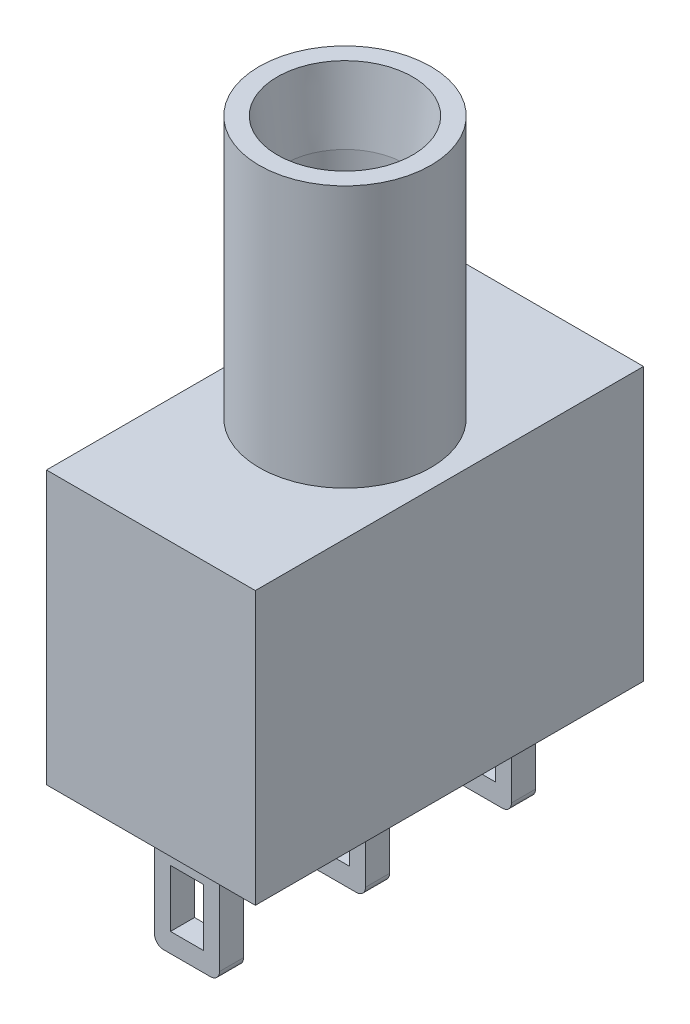
SolidWorks part; units mm, degrees
ref_plane "Plan de face" through (0, 0, 0) normal (0, 0, 1) x (1, 0, 0)
ref_plane "Plan de dessus" through (0, 0, 0) normal (0, 1, 0) x (1, 0, 0)
ref_plane "Plan de droite" through (0, 0, 0) normal (1, 0, 0) x (0, 0, -1)
sketch "Esquisse1" plane through (0, 0, 0) normal (0, 1, 0) x (1, 0, 0)
  line L1 (0, 0) -> (6.94, 0)
  line L2 (0, 0) -> (0, 12.9)
  line L3 (0, 12.9) -> (6.94, 12.9)
  line L4 (6.94, 0) -> (6.94, 12.9)
  dimension "D1" = 12.9
  dimension "D2" = 6.94
extrude "Boss.-Extru.1" add sketch "Esquisse1" along normal blind 9.06
sketch "Esquisse2" plane through (0, 9.06, 0) normal (0, 1, 0) x (1, 0, 0)
  line L0 (3.47, 12.9) -> (3.47, 0) construction
  line L1 (6.94, 12.9) -> (0, 12.9) construction
  line L2 (0, 0) -> (6.94, 0) construction
  circle A0 centre (3.47, 6.45) radius 2.85
  dimension "D1" = 5.7
extrude "Boss.-Extru.2" add sketch "Esquisse2" along normal blind 8.7
sketch "Esquisse3" plane through (0, 17.76, 0) normal (0, 1, 0) x (1, 0, 0)
  circle A0 centre (3.47, 6.45) radius 2
  dimension "D1" = 4
extrude "Enlèv. mat.-Extru.1" cut sketch "Esquisse3" against normal blind 8.7
sketch "Esquisse4" plane through (0, 0, 0) normal (-1, 0, 0) x (0, 0, 1)
  line L0 (-6.45, 0) -> (-6.45, 19.6396) construction
  line L1 (-12.9, 0) -> (0, 0) construction
  line L2 (-3.6, 17.76) -> (-9.3, 17.76) construction
  circle A0 centre (-6.4533, 14.76) radius 0.5
  dimension "D2" = 1
  dimension "D1" = 3
extrude "Enlèv. mat.-Extru.2" cut sketch "Esquisse4" against normal blind 2.5 and the other way blind 2.5 from offset 3.45 offset against normal yes
chamfer "Chanfrein1" distance 0.25 angle 84 1 edges at (3.47, 17.76, -4.45)
sketch "Esquisse5" plane through (0, 0, 0) normal (0, -1, 0) x (1, 0, 0)
  line L0 (6.94, -6.45) -> (-2.0351, -6.45) construction
  line L1 (6.94, 0) -> (6.94, -12.9) construction
  line L2 (3.47, 0) -> (3.47, -13.3292) construction
  line L3 (2.39, -1.2) -> (4.55, -1.2)
  line L4 (2.39, -1.2) -> (2.39, -2)
  line L5 (2.39, -2) -> (4.55, -2)
  line L6 (4.55, -1.2) -> (4.55, -2)
  line L7 (0, 0) -> (6.94, 0) construction
  line L8 (4.55, -11.7) -> (4.55, -10.9)
  line L9 (2.39, -10.9) -> (4.55, -10.9)
  line L10 (2.39, -11.7) -> (2.39, -10.9)
  line L11 (2.39, -11.7) -> (4.55, -11.7)
  line L13 (2.39, -6.05) -> (4.55, -6.05)
  line L14 (2.39, -6.05) -> (2.39, -6.85)
  line L15 (2.39, -6.85) -> (4.55, -6.85)
  line L16 (4.55, -6.05) -> (4.55, -6.85)
  dimension "D1" = 2.16
  dimension "D2" = 1.08
  dimension "D3" = 0.8
  dimension "D4" = 1.2
  dimension "D5" = 1.08
  dimension "D6" = 2.16
  dimension "D7" = 0.4
  dimension "D8" = 0.8
extrude "Boss.-Extru.3" add sketch "Esquisse5" along normal blind 4
fillet "Congé1" radius 0.3 6 edges at (4.55, -4, -11.3) (4.55, -4, -6.45) (4.55, -4, -1.6) (2.39, -4, -1.6) (2.39, -4, -6.45) (2.39, -4, -11.3)
sketch "Esquisse6" plane through (0, 0, -11.7) normal (0, 0, -1) x (-1, 0, 0)
  line L0 (-2.69, -4) -> (-4.25, -4) construction
  line L1 (-4.0203, -1.46) -> (-2.9203, -1.46)
  line L2 (-4.0203, -1.46) -> (-4.0203, -3.36)
  line L3 (-4.0203, -3.36) -> (-2.9203, -3.36)
  line L4 (-2.9203, -1.46) -> (-2.9203, -3.36)
  line L5 (-3.47, -4) -> (-3.47, -0.5723) construction
  dimension "D1" = 1.1
  dimension "D2" = 1.9
  dimension "D3" = 0.64
  dimension "D4" = 0.5497
extrude "Enlèv. mat.-Extru.3" cut sketch "Esquisse6" against normal through all
scale "Scale1" scale about centroid uniform scaling yes scale factor 0.64015
